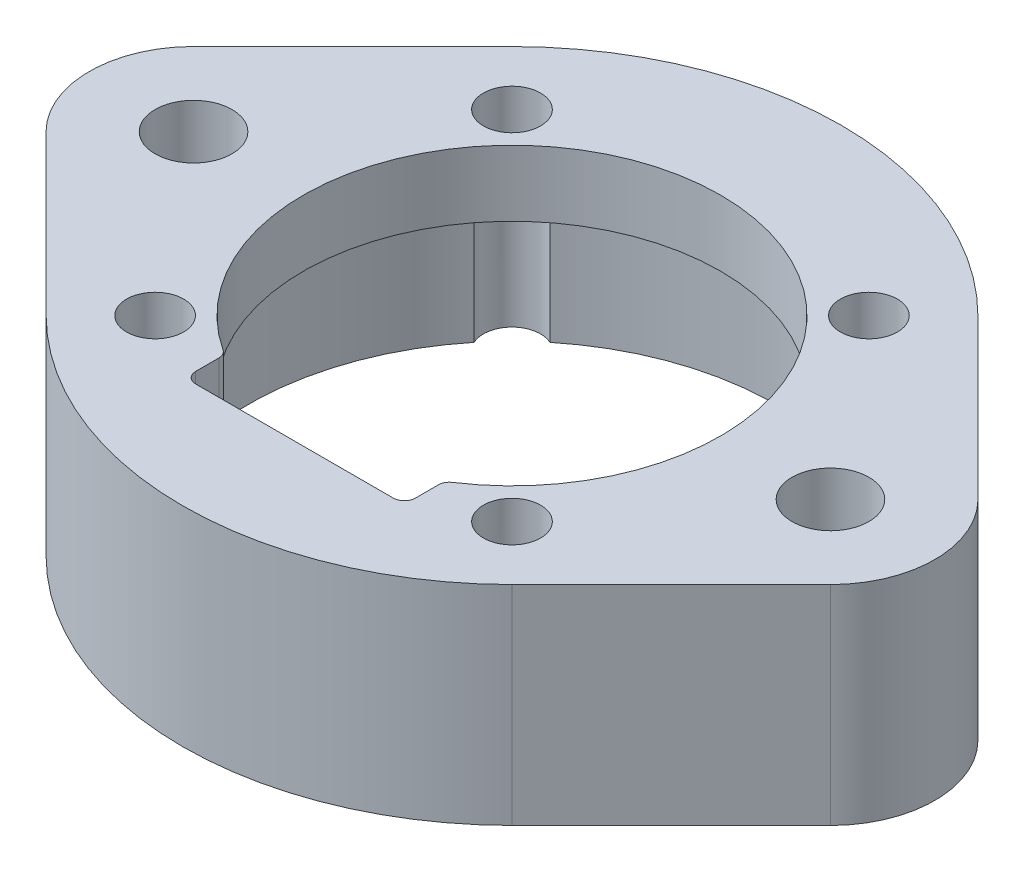
SolidWorks part; units mm, degrees
material "ABS"
ref_plane "Front Plane" through (0, 0, 0) normal (0, 0, 1) x (1, 0, 0)
ref_plane "Top Plane" through (0, 0, 0) normal (0, 1, 0) x (1, 0, 0)
ref_plane "Right Plane" through (0, 0, 0) normal (1, 0, 0) x (0, 0, -1)
sketch "Sketch1" plane through (0, 0, 0) normal (0, 1, 0) x (1, 0, 0)
  line L0 (0, 15) -> (0, -15) construction
  line L1 (-17.8578, 3.3598) -> (-10.6034, 10.6098)
  line L2 (0, 0) -> (-14.5, 0) construction
  line L3 (-17.8578, -3.3598) -> (-10.6034, -10.6098)
  line L4 (17.8578, 3.3598) -> (10.6034, 10.6098)
  line L5 (17.8578, -3.3598) -> (10.6034, -10.6098)
  arc A0 (-10.6034, -10.6098) -> (10.6034, -10.6098) centre (0, 0) ccw
  circle A1 centre (0, 0) radius 12
  circle A2 centre (-14.5, 0) radius 1.75
  arc A3 (-17.8578, 3.3598) -> (-17.8578, -3.3598) centre (-14.5, 0) ccw
  circle A4 centre (14.5, 0) radius 1.75
  arc A5 (17.8578, 3.3598) -> (17.8578, -3.3598) centre (14.5, 0) cw
  arc A6 (10.6034, 10.6098) -> (-10.6034, 10.6098) centre (0, 0) ccw
  point P25 (0, 0)
  dimension "D1" = 30
  dimension "D2" = 24
  dimension "D3" = 3.5
  dimension "D4" = 14.5
  dimension "D5" = 3
extrude "Boss-Extrude1" add sketch "Sketch1" along normal blind 9.5
sketch "Sketch3" plane through (0, 9.5, 0) normal (0, 1, 0) x (1, 0, 0)
  circle A0 centre (0, 0) radius 12 construction
  circle A1 centre (0, 0) radius 12
  circle A2 centre (0, 0) radius 9.5
  dimension "D1" = 19
extrude "Boss-Extrude2" add sketch "Sketch3" against normal blind 3
sketch "Sketch4" plane through (0, 9.5, 0) normal (0, 1, 0) x (1, 0, 0)
  line L1 (8.125, -8.125) -> (-8.125, -8.125) construction
  line L2 (8.125, -8.125) -> (8.125, 8.125) construction
  line L3 (8.125, 8.125) -> (-8.125, 8.125) construction
  line L4 (-8.125, -8.125) -> (-8.125, 8.125) construction
  line L5 (8.125, -8.125) -> (-8.125, 8.125) construction
  line L6 (8.125, 8.125) -> (-8.125, -8.125) construction
  circle A0 centre (8.125, 8.125) radius 1.3
  circle A1 centre (-8.125, 8.125) radius 1.3
  circle A2 centre (-8.125, -8.125) radius 1.3
  circle A3 centre (8.125, -8.125) radius 1.3
  point P0 (0, 0)
  dimension "D1" = 2.6
  dimension "D2" = 16.25
extrude "Cut-Extrude1" cut sketch "Sketch4" against normal through all
sketch "Sketch5" plane through (0, 9.5, 0) normal (0, 1, 0) x (1, 0, 0)
  line L0 (0, 0) -> (0, -7.4) construction
  line L2 (-5, -9.9) -> (5, -9.9)
  line L3 (-5, -9.9) -> (-5, -4.9)
  line L4 (-5, -4.9) -> (5, -4.9)
  line L5 (5, -9.9) -> (5, -4.9)
  line L6 (-5, -9.9) -> (5, -4.9) construction
  line L7 (-5, -4.9) -> (5, -9.9) construction
  dimension "D1" = 7.4
  dimension "D2" = 5
  dimension "D3" = 10
extrude "Cut-Extrude2" cut sketch "Sketch5" against normal up to surface (3 mm away) up to face at (0, 6.5, 9.5)
fillet "Fillet1" radius 0.5 4 edges at (5, 8, 8.0777) (5, 8, 9.9) (-5, 8, 9.9) (-5, 8, 8.0777)
